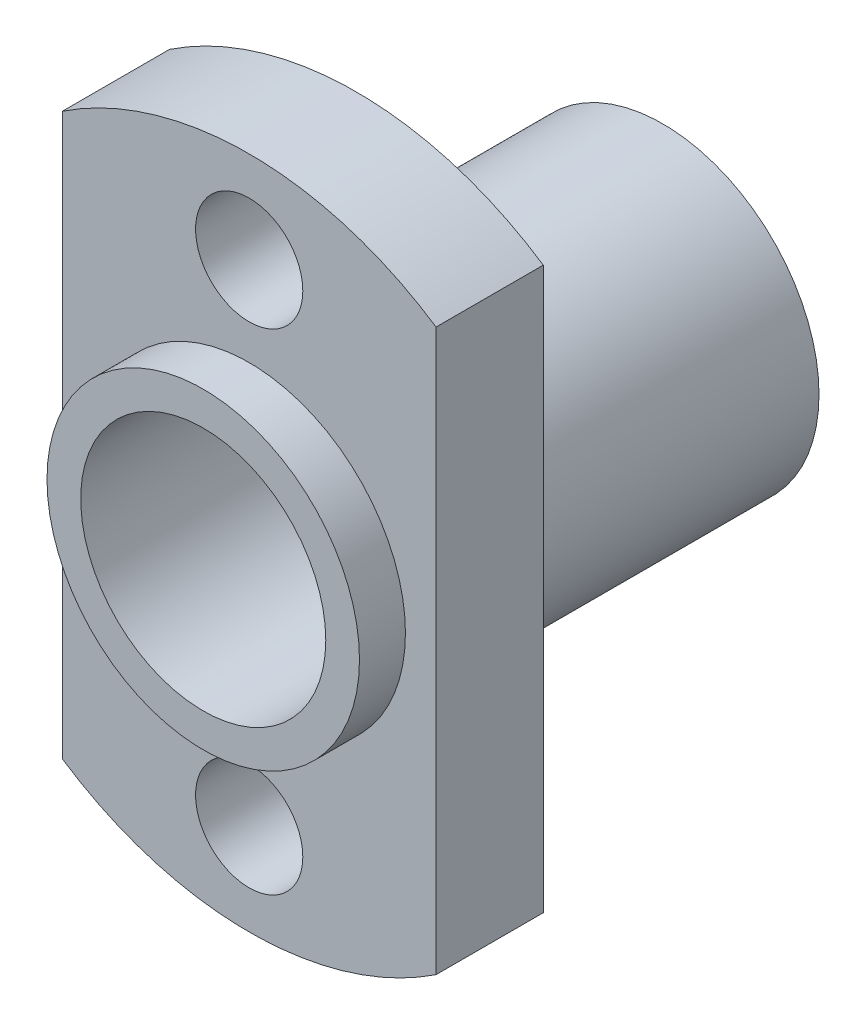
SolidWorks part; units mm, degrees
material "Brass"
ref_plane "Front Plane" through (0, 0, 0) normal (0, 0, 1) x (1, 0, 0)
ref_plane "Top Plane" through (0, 0, 0) normal (0, 1, 0) x (1, 0, 0)
ref_plane "Right Plane" through (0, 0, 0) normal (1, 0, 0) x (0, 0, -1)
sketch "Sketch1" plane through (0, 0, 0) normal (0, 0, 1) x (1, 0, 0)
  line L0 (-6.1, -9.1537) -> (-6.1, 9.1537)
  line L1 (6.1, -9.1537) -> (6.1, 9.1537)
  arc A0 (6.1, 9.1537) -> (-6.1, 9.1537) centre (0, 0) ccw
  circle A1 centre (0, 0) radius 5.1
  circle A2 centre (0, 0) radius 8 construction
  circle A3 centre (0, 8) radius 1.75
  arc A4 (-6.1, -9.1537) -> (6.1, -9.1537) centre (0, 0) ccw
  circle A5 centre (0, -8) radius 1.75
  circle A7 centre (-8, 0) radius 1.75 [skipped]
  circle A8 centre (8, 0) radius 1.75 [skipped]
  point P16 (0, 0)
  dimension "D1" = 22
  dimension "D2" = 10.2
  dimension "D3" = 16
  dimension "D4" = 3.5
  dimension "D6" = 6.1
  dimension "D7" = 6.1
  dimension "D5" = 4
extrude "Boss-Extrude1" add sketch "Sketch1" against normal blind 3.5
sketch "Sketch2" plane through (0, 0, 0) normal (0, 0, 1) x (1, 0, 0)
  circle A0 centre (0, 0) radius 5.1
  circle A1 centre (0, 0) radius 4
  dimension "D1" = 8
extrude "Boss-Extrude2" add sketch "Sketch2" along normal blind 1.5 and the other way blind 13.5
sketch "Sketch3" plane through (0, 0, 1.5) normal (0, 0, 1) x (1, 0, 0)
  circle A0 centre (0, 0) radius 4
curve "Helix/Spiral1" pitch 2 height 15 turns 7.5
sketch "Sketch4" plane through (0, 0, 0) normal (0, 1, 0) x (1, 0, 0)
  line L0 (3, -0.55) -> (3, -2.45)
  line L1 (3, -2.45) -> (5, -1.7146)
  line L2 (5, -1.7146) -> (5, -1.2854)
  line L3 (5, -1.2854) -> (3, -0.55)
  line L4 (3, -1.5) -> (5, -1.5)
  point P6 (4, -1.5)
  dimension "D1" = 1.9
  dimension "D2" = 2
  dimension "D3" = 69.811
